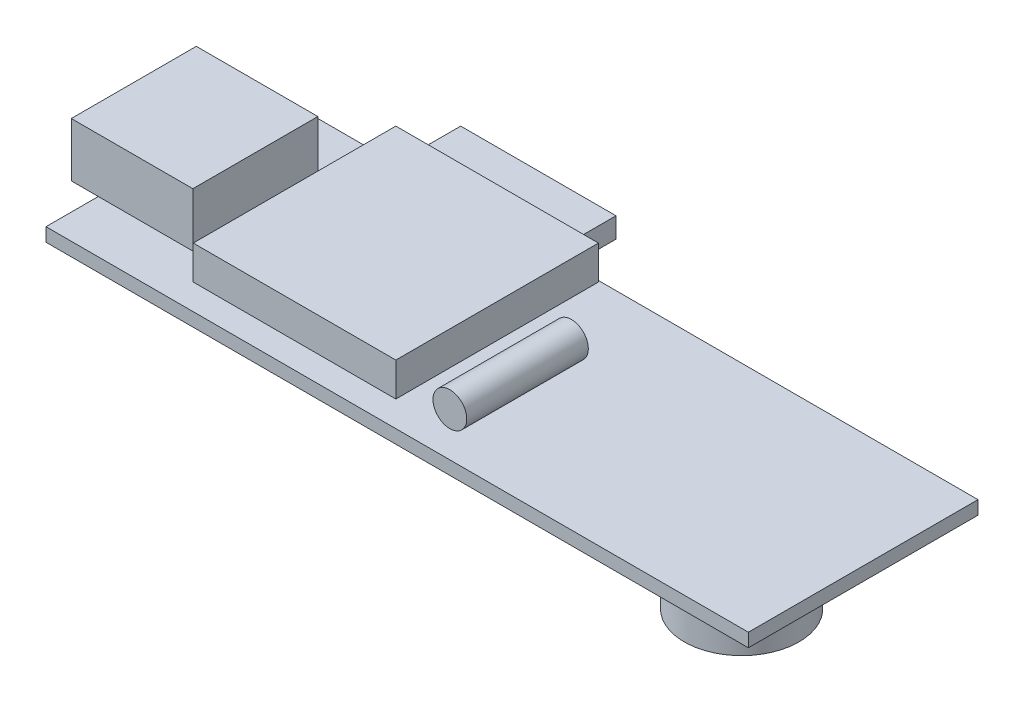
SolidWorks part; units mm, degrees
ref_plane "Front Plane" through (0, 0, 0) normal (0, 0, 1) x (1, 0, 0)
ref_plane "Top Plane" through (0, 0, 0) normal (0, 1, 0) x (1, 0, 0)
ref_plane "Right Plane" through (0, 0, 0) normal (1, 0, 0) x (0, 0, -1)
sketch "Sketch1" plane through (0, 0, 0) normal (0, 1, 0) x (1, 0, 0)
  line L1 (-520, 290.2516) -> (-468, 290.2516)
  line L2 (-520, 290.2516) -> (-520, 273.2516)
  line L3 (-520, 273.2516) -> (-468, 273.2516)
  line L4 (-468, 290.2516) -> (-468, 273.2516)
  line L5 (-520, 290.2516) -> (-468, 273.2516) construction
  line L6 (-520, 273.2516) -> (-468, 290.2516) construction
  point P0 (-494, 281.7516)
  dimension "D1" = 52
  dimension "D2" = 17
extrude "Boss-Extrude1" add sketch "Sketch1" along normal blind 1
sketch "Sketch2" plane through (0, 1, 0) normal (0, 1, 0) x (1, 0, 0)
  line L1 (-522, 286.3793) -> (-513, 286.3793)
  line L2 (-522, 286.3793) -> (-522, 277.1238)
  line L3 (-522, 277.1238) -> (-513, 277.1238)
  line L4 (-468, 273.2516) -> (-468, 290.2516)
  line L5 (-468, 290.2516) -> (-520, 290.2516)
  line L6 (-520, 290.2516) -> (-520, 273.2516)
  line L7 (-520, 273.2516) -> (-468, 273.2516)
  line L8 (-468, 273.2516) -> (-468, 290.2516)
  line L9 (-468, 290.2516) -> (-520, 290.2516)
  line L10 (-520, 290.2516) -> (-520, 273.2516)
  line L11 (-520, 273.2516) -> (-468, 273.2516)
  line L12 (-513, 286.3793) -> (-513, 277.1238)
  line L13 (-522, 286.3793) -> (-513, 277.1238) construction
  line L14 (-522, 277.1238) -> (-513, 286.3793) construction
  point P2 (-517.5, 281.7516)
  line M11 (-520, 290.2516) -> (-520, 273.2516)
  dimension "D2" = 9
  dimension "D3" = 9.2555
  dimension "D4" = 2
  dimension "D1" = 0
extrude "Boss-Extrude2" add sketch "Sketch2" along normal blind 4 contours L2 L3 L1 M11 | L12 L1 L3 M11
sketch "Sketch3" plane through (0, 1, 0) normal (0, 1, 0) x (1, 0, 0)
  line L0 (-520, 290.2516) -> (-520, 286.3793) construction
  line L1 (-496, 275.1516) -> (-511, 275.1516)
  line L2 (-496, 275.1516) -> (-496, 290.1516)
  line L3 (-496, 290.1516) -> (-511, 290.1516)
  line L4 (-511, 275.1516) -> (-511, 290.1516)
  line L6 (-468, 290.2516) -> (-520, 290.2516) construction
  dimension "D1" = 9
  dimension "D2" = 15
  dimension "D3" = 15
  dimension "D4" = 0.1
extrude "Boss-Extrude3" add sketch "Sketch3" along normal blind 2.5
sketch "Sketch4" plane through (0, 0, -290.1516) normal (0, 0, -1) x (-1, 0, 0)
  line L0 (496, 3.5) -> (496, 1) construction
  line L1 (508.7, 1.9) -> (497.2, 1.9)
  line L2 (508.7, 1.9) -> (508.7, 3.4)
  line L3 (508.7, 3.4) -> (497.2, 3.4)
  line L4 (497.2, 1.9) -> (497.2, 3.4)
  line L5 (496, 3.5) -> (511, 3.5) construction
  dimension "D1" = 1.2
  dimension "D2" = 11.5
  dimension "D3" = 1.5
  dimension "D4" = 0.1
extrude "Boss-Extrude4" add sketch "Sketch4" along normal blind 2.5
sketch "Sketch5" plane through (0, 0, -275.1516) normal (0, 0, 1) x (1, 0, 0)
  line L0 (-520, 1) -> (-468, 1) construction
  line L1 (-520, 1) -> (-468, 1)
  line L6 (-511, 1) -> (-496, 1)
  line L7 (-496, 1) -> (-496, 3.5)
  line L8 (-496, 3.5) -> (-511, 3.5)
  line L9 (-511, 3.5) -> (-511, 1)
  line L10 (-511, 1) -> (-496, 1)
  line L11 (-496, 1) -> (-496, 3.5)
  line L12 (-496, 3.5) -> (-511, 3.5)
  line L13 (-511, 3.5) -> (-511, 1)
  circle A0 centre (-492, 2.35) radius 1.25
  dimension "D2" = 2.5
  dimension "D3" = 4
  dimension "D4" = 1.35
  dimension "D1" = 0
extrude "Boss-Extrude5" add sketch "Sketch5" against normal blind 9 separate body contours A0
sketch "Sketch6" plane through (0, 0, 0) normal (0, -1, 0) x (1, 0, 0)
  line L1 (-473, -277.7516) -> (-481.5, -277.7516)
  line L2 (-473, -277.7516) -> (-473, -286.2516)
  line L3 (-473, -286.2516) -> (-481.5, -286.2516)
  line L4 (-481.5, -277.7516) -> (-481.5, -286.2516)
  line L6 (-520, -273.2516) -> (-468, -273.2516) construction
  line L7 (-468, -273.2516) -> (-468, -290.2516) construction
  dimension "D1" = 8.5
  dimension "D2" = 8.5
  dimension "D3" = 4.5
  dimension "D4" = 5
extrude "Boss-Extrude6" add sketch "Sketch6" along normal blind 3.5
sketch "Sketch7" plane through (0, -3.5, 0) normal (0, -1, 0) x (1, 0, 0)
  line L0 (-473, -286.2516) -> (-481.5, -277.7516) construction
  line L1 (-473, -277.7516) -> (-481.5, -286.2516) construction
  line L4 (-473, -286.2516) -> (-473, -277.7516)
  line L5 (-473, -277.7516) -> (-481.5, -277.7516)
  line L6 (-481.5, -277.7516) -> (-481.5, -286.2516)
  line L7 (-481.5, -286.2516) -> (-473, -286.2516)
  line L8 (-473, -286.2516) -> (-473, -277.7516)
  line L9 (-473, -277.7516) -> (-481.5, -277.7516)
  line L10 (-481.5, -277.7516) -> (-481.5, -286.2516)
  line L11 (-481.5, -286.2516) -> (-473, -286.2516)
  circle A0 centre (-477.25, -282.0016) radius 4.25
  dimension "D1" = 0
extrude "Boss-Extrude7" add sketch "Sketch7" along normal blind 3 contours A0
sketch "Sketch8" plane through (0, 0, 0) normal (0, -1, 0) x (-1, 0, 0)
  line L1 (503.6398, 286.1063) -> (492.0958, 286.1063)
  line L2 (503.6398, 286.1063) -> (503.6398, 277.2478)
  line L3 (503.6398, 277.2478) -> (492.0958, 277.2478)
  line L4 (492.0958, 286.1063) -> (492.0958, 277.2478)
extrude "Boss-Extrude8" add sketch "Sketch8" along normal blind 2
sketch "Sketch12" plane through (0, -6.5, 0) normal (0, -1, 0) x (1, 0, 0)
  line L0 (-468, -281.7516) -> (-520, -281.7516) construction
  line L4 (-468, -290.2516) -> (-468, -273.2516)
  line L5 (-468, -273.2516) -> (-520, -273.2516)
  line L6 (-520, -273.2516) -> (-520, -290.2516)
  line L7 (-520, -290.2516) -> (-468, -290.2516)
  line L8 (-468, -290.2516) -> (-468, -273.2516)
  line L9 (-468, -273.2516) -> (-520, -273.2516)
  line L10 (-520, -273.2516) -> (-520, -290.2516)
  line L11 (-520, -290.2516) -> (-468, -290.2516)
  dimension "D1" = 0
